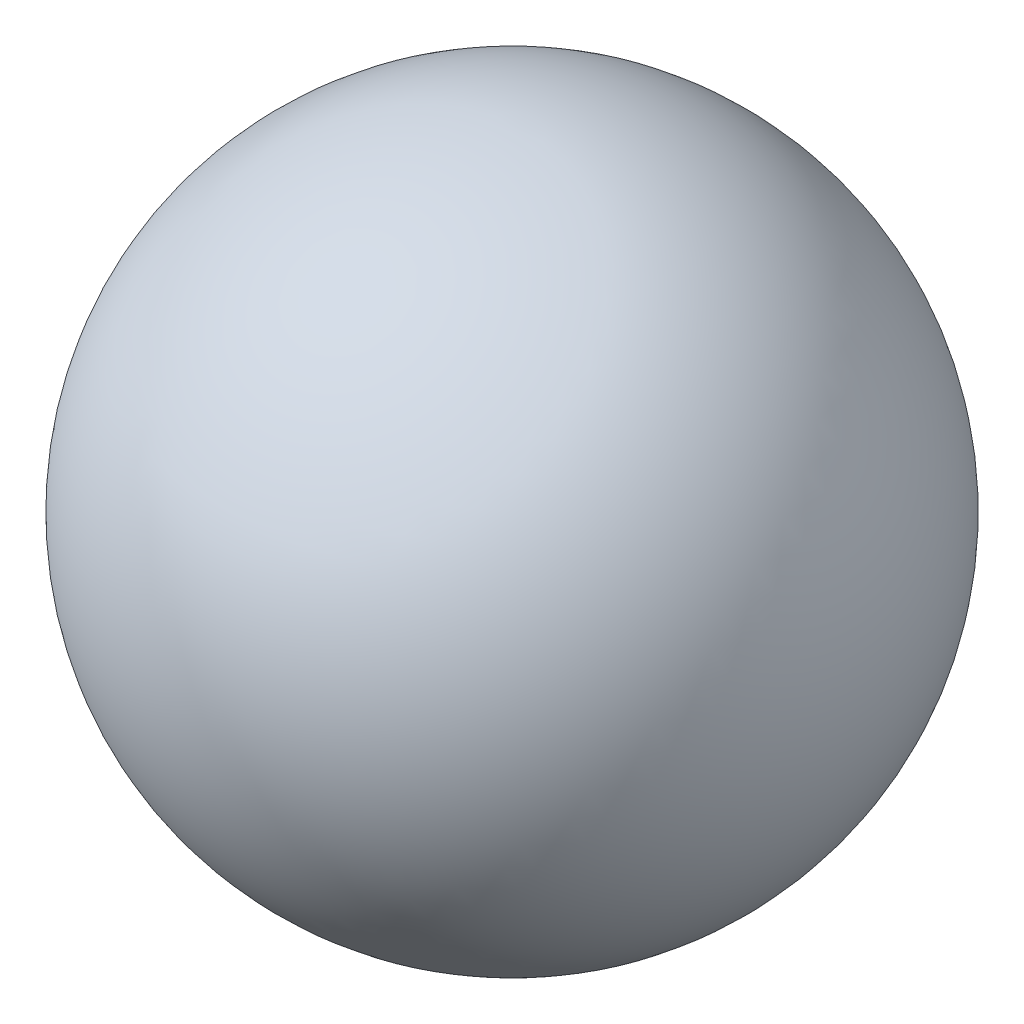
SolidWorks part; units mm, degrees
material "Nylon 101"
ref_plane "Front Plane" through (0, 0, 0) normal (0, 0, 1) x (1, 0, 0)
ref_plane "Top Plane" through (0, 0, 0) normal (0, 1, 0) x (1, 0, 0)
ref_plane "Right Plane" through (0, 0, 0) normal (1, 0, 0) x (0, 0, -1)
sketch "Sketch1" plane through (0, 0, 0) normal (0, 0, 1) x (1, 0, 0)
  line L0 (-2.3813, 0) -> (2.3813, 0) construction
  point P4 (0, 0)
  dimension "Diameter" = 4.7625
sketch "Sketch2" plane through (0, 0, 0) normal (0, 0, 1) x (1, 0, 0)
  line L0 (0, 2.3813) -> (0, -2.3813)
  circle A0 centre (0, 0) radius 2.3813 construction
  arc A1 (0, 2.3813) -> (0, -2.3813) centre (0, 0) cw
revolve "Revolve1" add sketch "Sketch2" angle 360 about L0
